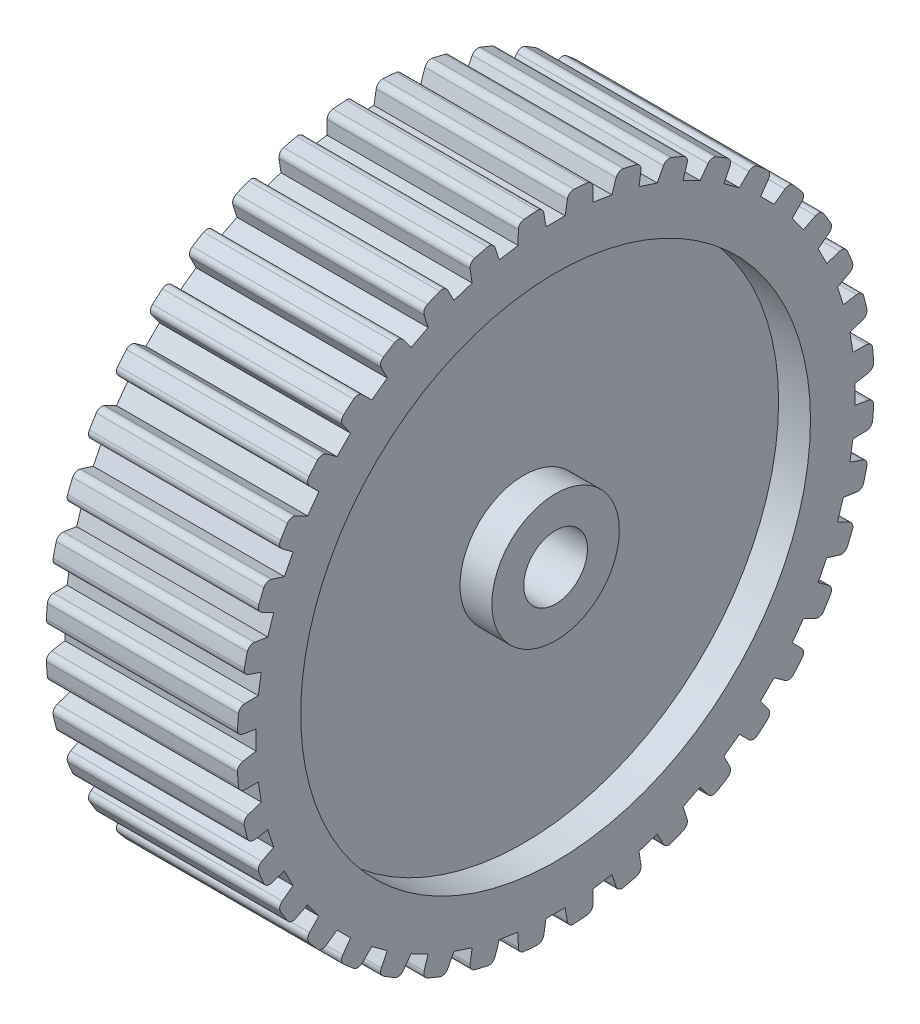
SolidWorks part; units mm, degrees
ref_plane "Front Plane" through (0, 0, 0) normal (0, 0, 1) x (1, 0, 0)
ref_plane "Top Plane" through (0, 0, 0) normal (0, 1, 0) x (1, 0, 0)
ref_plane "Right Plane" through (0, 0, 0) normal (1, 0, 0) x (0, 0, -1)
sketch "Sketch1" plane through (0, 0, 0) normal (0, 0, 1) x (1, 0, 0)
  line L0 (0, 0) -> (-34.486, 0) construction
  line L1 (0, 5) -> (-30, 5)
  line L2 (-30, 5) -> (-30, 10)
  line L3 (-30, 10) -> (-25, 10)
  line L4 (-25, 10) -> (-25, 40)
  line L5 (-25, 40) -> (-30, 40)
  line L6 (-30, 40) -> (-30, 50)
  line L7 (-30, 50) -> (0, 50)
  line L8 (0, 50) -> (0, 40)
  line L9 (0, 40) -> (-5, 40)
  line L10 (-5, 40) -> (-5, 10)
  line L11 (-5, 10) -> (0, 10)
  line L12 (0, 10) -> (0, 5)
  point P5 (0, 0)
  point P16 (0, 0)
  point P17 (0, 0)
  dimension "D1" = 10
  dimension "D2" = 100
  dimension "D3" = 30
  dimension "D4" = 20
  dimension "D5" = 5
  dimension "D6" = 10
revolve "Revolve1" add sketch "Sketch1" angle 360 about L0
sketch "Sketch2" plane through (0, 0, 0) normal (1, 0, 0) x (0, 0, -1)
  line L0 (-2.5, 53) -> (-1.5, 47)
  line L1 (-1.5, 47) -> (1.5, 47)
  line L2 (1.5, 47) -> (2.5, 53)
  line L3 (2.5, 53) -> (-2.5, 53)
  circle A0 centre (0, 0) radius 50 construction
  point P2 (0, 47)
  point P5 (0, 53)
  point P7 (0, 50)
  point P8 (1.5, 48.2087)
  dimension "D1" = 3
  dimension "D2" = 5
  dimension "D3" = 6
  dimension "D4" = 3
extrude "Cut-Extrude1" cut sketch "Sketch2" against normal blind 44
fillet "Fillet1" radius 1 2 edges at (-15, 49.9602, 1.9934) (-15, 49.9602, -1.9934)
pattern_circular "CirPattern1" count 40 over 360 about axis through (0, 0, 0) along (1, 0, 0) of "Cut-Extrude1", "Fillet1"
